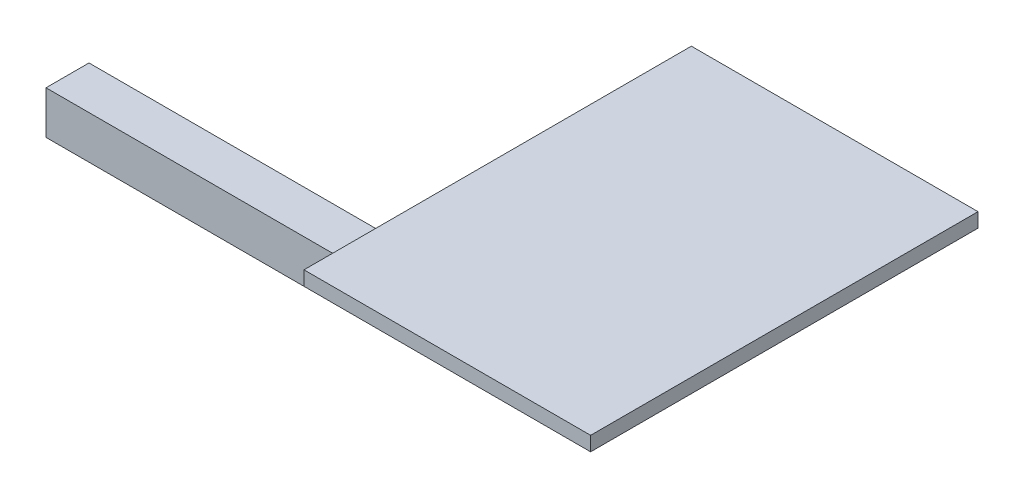
SolidWorks part; units mm, degrees
ref_plane "Front Plane" through (0, 0, 0) normal (0, 0, 1) x (1, 0, 0)
ref_plane "Top Plane" through (0, 0, 0) normal (0, 1, 0) x (1, 0, 0)
ref_plane "Right Plane" through (0, 0, 0) normal (1, 0, 0) x (0, 0, -1)
sketch "Sketch1" plane through (0, 0, 0) normal (0, 1, 0) x (1, 0, 0)
  line L1 (0, 0) -> (-200, 0)
  line L2 (0, 0) -> (0, 270.2852)
  line L3 (0, 270.2852) -> (-200, 270.2852)
  line L4 (-200, 0) -> (-200, 270.2852)
  dimension "D1" = 200
  dimension "D2" = 270.2852
extrude "Extrude1" add sketch "Sketch1" along normal blind 10
sketch "Sketch2" plane through (0, 0, 0) normal (0, -1, 0) x (1, 0, 0)
  line L0 (-200, -270.2852) -> (-200, 0) construction
  line L1 (-150, -130) -> (-120, -130)
  line L2 (-150, -130) -> (-150, -100)
  line L3 (-150, -100) -> (-120, -100)
  line L4 (-120, -130) -> (-120, -100)
  line L5 (-200, 0) -> (0, 0) construction
  dimension "D1" = 30
  dimension "D2" = 30
  dimension "D3" = 50
  dimension "D4" = 100
extrude "Extrude2" add sketch "Sketch2" along normal blind 100
sketch "Sketch3" plane through (-150, 0, 0) normal (-1, 0, 0) x (0, 0, 1)
  line L0 (-130, -100) -> (-130, 0) construction
  line L1 (-130, -70) -> (-100, -70)
  line L2 (-130, -70) -> (-130, -100)
  line L3 (-130, -100) -> (-100, -100)
  line L4 (-100, -70) -> (-100, -100)
  dimension "D1" = 30
extrude "Extrude3" add sketch "Sketch3" along normal blind 330
